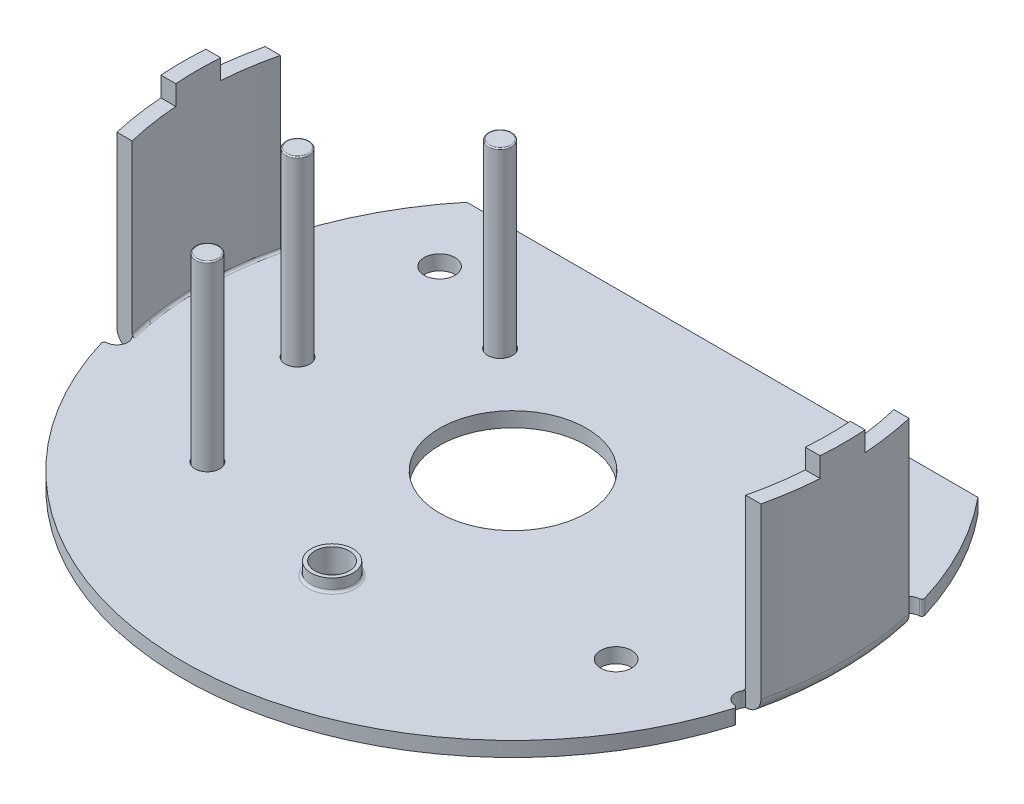
SolidWorks part; units mm, degrees
material "Ст. 3кп ГОСТ 380-2005"
ref_plane "Спереди" through (0, 0, 0) normal (0, 0, 1) x (1, 0, 0)
ref_plane "Сверху" through (0, 0, 0) normal (0, 1, 0) x (1, 0, 0)
ref_plane "Справа" through (0, 0, 0) normal (1, 0, 0) x (0, 0, -1)
sketch "Эскиз1" plane through (0, 0, 0) normal (0, 1, 0) x (1, 0, 0)
  circle A0 centre (0, 0) radius 13.375
  dimension "D1" = 26.75
extrude "Бобышка-Вытянуть1" add sketch "Эскиз1" along normal blind 7.85
shell "Оболочка1" thickness 0.6
sketch "Эскиз2" plane through (0, 7.85, 0) normal (0, 1, 0) x (1, 0, 0)
  line L0 (0, 8.475) -> (0, 0) construction
  line L1 (-13.375, 14) -> (13.375, 14)
  line L2 (-13.375, 14) -> (-13.375, 8.475)
  line L3 (-13.375, 8.475) -> (13.375, 8.475)
  line L4 (13.375, 14) -> (13.375, 8.475)
  circle A0 centre (0, 0) radius 13.375 construction
  dimension "D1" = 14
  dimension "D2" = 21.85
extrude "Вырез-Вытянуть1" cut sketch "Эскиз2" against normal up to surface (7.85 mm away) up to face at (0, 0, 13.375)
sketch "Эскиз3" plane through (0, 7.85, 0) normal (0, 1, 0) x (1, 0, 0)
  line L0 (0, 3) -> (0, 0) construction
  line L1 (-13.375, 9.475) -> (13.375, 9.475)
  line L2 (-13.375, 9.475) -> (-13.375, 3)
  line L3 (-13.375, 3) -> (13.375, 3)
  line L4 (13.375, 9.475) -> (13.375, 3)
  line L5 (-13.375, -3) -> (13.375, -3)
  line L6 (-13.375, -3) -> (-13.375, -14.375)
  line L7 (-13.375, -14.375) -> (13.375, -14.375)
  line L8 (13.375, -3) -> (13.375, -14.375)
  line L9 (0, 0) -> (0, -3) construction
  line L10 (-9.559, 8.475) -> (9.559, 8.475) construction
  arc A0 (-10.3472, 8.475) -> (10.3472, 8.475) centre (0, 0) ccw construction
  dimension "D3" = 1
  dimension "D1" = 6
  dimension "D2" = 1
extrude "Вырез-Вытянуть2" cut sketch "Эскиз3" against normal up to surface (7.25 mm away) up to face at (0, 0.6, 2.15)
sketch "Эскиз4" plane through (0, 0.6, 0) normal (0, 1, 0) x (1, 0, 0)
  line L0 (-13.0342, -3) -> (-12.4178, -3) construction
  line L1 (-13.0342, 3) -> (-12.4178, 3) construction
  line L2 (-13.0342, -3) -> (-12.4178, -3)
  line L3 (-13.0342, 3) -> (-12.4178, 3)
  arc A0 (-12.4178, 3) -> (-12.8469, 3.7212) centre (-12.7342, 3.3) ccw
  arc A1 (-10.3472, 8.475) -> (-13.0342, 3) centre (0, 0) ccw construction
  arc A2 (-12.4178, -3) -> (-12.8469, -3.7212) centre (-12.7342, -3.3) cw
  arc A3 (-13.0342, -3) -> (13.0342, -3) centre (0, 0) ccw construction
  arc A4 (-13.0342, -3) -> (-12.8469, -3.7212) centre (0, 0) ccw
  arc A5 (-12.8469, 3.7212) -> (-13.0342, 3) centre (0, 0) ccw
  dimension "D1" = 0.3
  dimension "D2" = 0.3
  dimension "D3" = 0.3
extrude "Вырез-Вытянуть3" cut sketch "Эскиз4" against normal up to surface (0.6 mm away) up to face at (0, 0, 2.45)
mirror "Зеркальное отражение1" about plane through (0, 0, 0) normal (1, 0, 0) of "Вырез-Вытянуть3"
fillet "Скругление1" radius 0.1 4 edges at (12.8469, 0.3, 3.7212) (12.8469, 0.3, -3.7212) (-12.8469, 0.3, -3.7212) (-12.8469, 0.3, 3.7212)
fillet "Скругление2" radius 0.6 2 edges at (-13.375, 0, 0) (13.375, 0, 0)
fillet "Скругление3" radius 0.1 2 edges at (-12.775, 0.6, 0) (12.775, 0.6, 0)
sketch "Эскиз5" plane through (0, 0.6, 0) normal (0, 1, 0) x (1, 0, 0)
  line L0 (-10.3472, 8.475) -> (10.3472, 8.475) construction
  circle A0 centre (0, 0) radius 2.975
  circle A1 centre (-8.6472, 5.675) radius 0.625
  circle A2 centre (-4.5472, 4.025) radius 0.5
  circle A3 centre (-8.3472, -0.375) radius 0.5
  circle A4 centre (-6.4972, -5.875) radius 0.5
  circle A5 centre (0, -7.325) radius 0.7
  circle A6 centre (8.6972, -4.525) radius 0.625
  dimension "D1" = 5.95
  dimension "D2" = 1
  dimension "D6" = 1.25
  dimension "D12" = 1.4
  dimension "D3" = 4.45
  dimension "D4" = 4.4
  dimension "D5" = 5.5
  dimension "D7" = 2.8
  dimension "D8" = 1.7
  dimension "D9" = 5.8
  dimension "D10" = 3.8
  dimension "D11" = 1.85
  dimension "D13" = 15.8
  dimension "D14" = 13
  dimension "D15" = 1.65
extrude "Вырез-Вытянуть4" cut sketch "Эскиз5" against normal up to surface (0.6 mm away) up to face at (0, 0, -0.5487)
sketch "Эскиз6" plane through (0, 0, 0) normal (0, -1, 0) x (1, 0, 0)
  circle A0 centre (-6.4972, 5.875) radius 1.1
  circle A1 centre (-8.3472, 0.375) radius 1.1
  circle A2 centre (-4.5472, -4.025) radius 1.1
  dimension "D1" = 2.2
extrude "Вырез-Вытянуть5" cut sketch "Эскиз6" against normal blind 0.1
sketch "Эскиз7" plane through (0, 0, 0) normal (0, -1, 0) x (1, 0, 0)
  circle A0 centre (-6.4972, 5.875) radius 0.475
  circle A1 centre (-8.3472, 0.375) radius 0.475
  circle A2 centre (-4.5472, -4.025) radius 0.475
  dimension "D1" = 0.95
extrude "Бобышка-Вытянуть2" add sketch "Эскиз7" against normal blind 7.95 separate body
fillet "Скругление4" radius 0.05 2 edges at (-4.5472, 7.95, -4.5) (-4.5472, 0, -4.5)
fillet "Скругление5" radius 0.05 2 edges at (-8.3472, 7.95, -0.1) (-8.3472, 0, -0.1)
fillet "Скругление6" radius 0.05 2 edges at (-6.4972, 0, 5.4) (-6.4972, 7.95, 5.4)
sketch "Эскиз8" plane through (0, 7.85, 0) normal (0, 1, 0) x (1, 0, 0)
  line L0 (-13.0342, 3) -> (-12.4178, 3) construction
  line L1 (-13.375, 3.1) -> (13.375, 3.1)
  line L2 (-13.375, 3.1) -> (-13.375, 0.91)
  line L3 (-13.375, 0.91) -> (13.375, 0.91)
  line L4 (13.375, 3.1) -> (13.375, 0.91)
  line L5 (-13.375, -0.91) -> (13.375, -0.91)
  line L6 (-13.375, -0.91) -> (-13.375, -3.1)
  line L7 (-13.375, -3.1) -> (13.375, -3.1)
  line L8 (13.375, -0.91) -> (13.375, -3.1)
  line L9 (-12.4178, -3) -> (-13.0342, -3) construction
  line L10 (0, 0) -> (0, 0.91) construction
  line L11 (0, 0) -> (0, -0.91) construction
  arc A0 (-13.0342, 3) -> (-13.0342, -3) centre (0, 0) ccw construction
  dimension "D1" = 0.1
  dimension "D2" = 0.1
  dimension "D3" = 1.82
extrude "Вырез-Вытянуть6" cut sketch "Эскиз8" against normal blind 0.4
sketch "Эскиз9" plane through (0, 7.85, 0) normal (0, 1, 0) x (1, 0, 0)
  line L2 (-13.344, -0.91) -> (-12.7425, -0.91)
  line L3 (-12.7425, 0.91) -> (-13.344, 0.91)
  line L4 (-13.344, -0.91) -> (-12.7425, -0.91)
  line L5 (-12.7425, 0.91) -> (-13.344, 0.91)
  line L6 (12.7425, -0.91) -> (13.344, -0.91)
  line L7 (13.344, 0.91) -> (12.7425, 0.91)
  line L8 (12.7425, -0.91) -> (13.344, -0.91)
  line L9 (13.344, 0.91) -> (12.7425, 0.91)
  arc A2 (-12.7425, 0.91) -> (-12.7425, -0.91) centre (0, 0) ccw
  arc A3 (-13.344, 0.91) -> (-13.344, -0.91) centre (0, 0) ccw
  arc A4 (-12.7425, 0.91) -> (-12.7425, -0.91) centre (0, 0) ccw
  arc A5 (-13.344, 0.91) -> (-13.344, -0.91) centre (0, 0) ccw
  arc A6 (13.344, -0.91) -> (13.344, 0.91) centre (0, 0) ccw
  arc A7 (12.7425, -0.91) -> (12.7425, 0.91) centre (0, 0) ccw
  arc A8 (13.344, -0.91) -> (13.344, 0.91) centre (0, 0) ccw
  arc A9 (12.7425, -0.91) -> (12.7425, 0.91) centre (0, 0) ccw
  dimension "D1" = 0
  dimension "D2" = 0
extrude "Бобышка-Вытянуть3" add sketch "Эскиз9" along normal blind 0.4
sketch "Эскиз10" plane through (0, 0.6, 0) normal (0, 1, 0) x (1, 0, 0)
  circle A0 centre (0, -7.325) radius 0.85
  circle A1 centre (0, -7.325) radius 0.7 construction
  circle A2 centre (0, -7.325) radius 0.7
  dimension "D1" = 0.15
extrude "Бобышка-Вытянуть4" add sketch "Эскиз10" along normal blind 0.5
fillet "Скругление7" radius 0.15 1 edges at (0, 0, 8.025)
fillet "Скругление8" radius 0.1 1 edges at (0, 0.6, 8.175)
